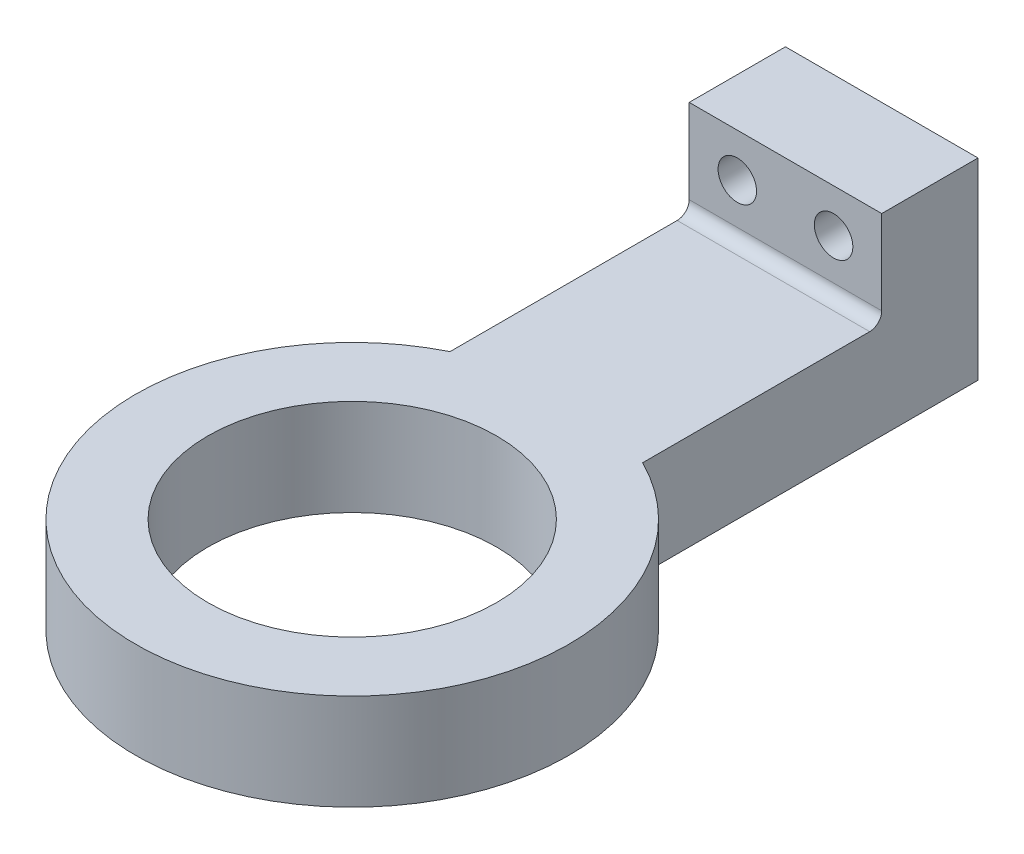
SolidWorks part; units mm, degrees
ref_plane "Front" through (0, 0, 0) normal (0, 0, 1) x (1, 0, 0)
ref_plane "Top" through (0, 0, 0) normal (0, 1, 0) x (1, 0, 0)
ref_plane "Right" through (0, 0, 0) normal (1, 0, 0) x (0, 0, -1)
sketch "Sketch1" plane through (0, 0, 0) normal (0, 1, 0) x (1, 0, 0)
  circle A0 centre (0, 0) radius 30
  circle A1 centre (0, 0) radius 45
  dimension "D1" = 90
  dimension "D2" = 60
extrude "Boss-Extrude1" add sketch "Sketch1" along normal blind 20
sketch "Sketch2" plane through (0, 0, 0) normal (0, 1, 0) x (1, 0, 0)
  line L1 (-20, 110) -> (20, 110)
  line L2 (-20, 110) -> (-20, 30)
  line L3 (-20, 30) -> (20, 30)
  line L4 (20, 110) -> (20, 30)
  line L5 (-20, 110) -> (20, 30) construction
  line L6 (-20, 30) -> (20, 110) construction
  circle A0 centre (0, 0) radius 30 construction
  point P0 (0, 70)
  point P7 (-9.8253, 81.9215)
  dimension "D1" = 40
  dimension "D2" = 80
extrude "Boss-Extrude2" add sketch "Sketch2" along normal up to surface (20 mm away) up to face at (0, 20, 45)
sketch "Sketch3" plane through (0, 20, 0) normal (0, 1, 0) x (1, 0, 0)
  line L0 (20, 40.3113) -> (20, 110) construction
  line L1 (-20, 90) -> (20, 90)
  line L2 (-20, 90) -> (-20, 110)
  line L3 (-20, 110) -> (20, 110)
  line L4 (20, 90) -> (20, 110)
  line L5 (-20, 90) -> (20, 110) construction
  line L6 (-20, 110) -> (20, 90) construction
  line L7 (20, 110) -> (-20, 110) construction
  point P0 (0, 100)
  point P9 (0, 0)
  dimension "D1" = 20
extrude "Boss-Extrude3" add sketch "Sketch3" along normal blind 20
fillet "Fillet1" radius 2.5 1 edges at (0, 20, -90)
sketch "Sketch4" plane through (0, 0, -90) normal (0, 0, 1) x (1, 0, 0)
  line L0 (20, 40) -> (20, 22.5) construction
  line L1 (-20, 40) -> (20, 40) construction
  line L2 (-20, 40) -> (-20, 22.5) construction
  circle A0 centre (10, 31) radius 4
  circle A1 centre (-10, 31) radius 4
  point P10 (0, 0)
  dimension "D1" = 8
  dimension "D2" = 10
  dimension "D3" = 9
  dimension "D4" = 10
extrude "Cut-Extrude1" cut sketch "Sketch4" against normal through all
